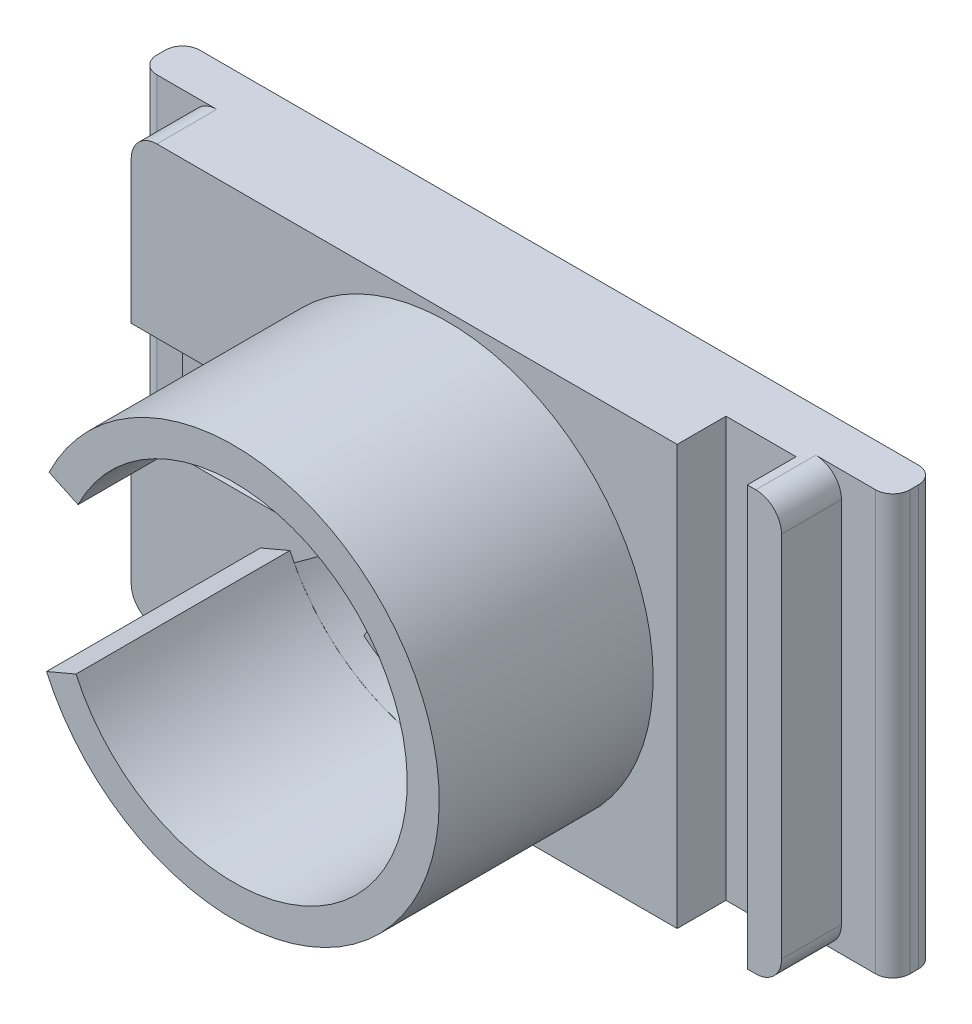
SolidWorks part; units mm, degrees
ref_plane "Front Plane" through (0, 0, 0) normal (0, 0, 1) x (1, 0, 0)
ref_plane "Top Plane" through (0, 0, 0) normal (0, 1, 0) x (1, 0, 0)
ref_plane "Right Plane" through (0, 0, 0) normal (1, 0, 0) x (0, 0, -1)
sketch "Sketch1" plane through (0, 0, 0) normal (0, 0, 1) x (1, 0, 0)
  line L1 (-32.5, -25) -> (32.5, -25)
  line L2 (-32.5, -25) -> (-32.5, 25)
  line L3 (-32.5, 25) -> (32.5, 25)
  line L4 (32.5, -25) -> (32.5, 25)
  line L5 (-32.5, -25) -> (32.5, 25) construction
  line L6 (-32.5, 25) -> (32.5, -25) construction
  point P0 (0, 0)
  dimension "D1" = 0
  dimension "D2" = 50
  dimension "D3" = 65
extrude "Boss-Extrude1" add sketch "Sketch1" along normal blind 12
sketch "Sketch2" plane through (0, 0, 12) normal (0, 0, 1) x (1, 0, 0)
  line L0 (32.5, -25) -> (32.5, 25) construction
  line L1 (-32.5, -25) -> (32.5, -25) construction
  line L2 (-1.6792, -18.9347) -> (-0.0792, -16.1634)
  line L3 (-44.0305, 5.35) -> (-14.0305, 5.35)
  line L4 (-44.0305, 5.35) -> (-44.0305, -5.35)
  line L5 (-44.0305, -5.35) -> (-14.0305, -5.35)
  line L6 (-14.0305, 5.35) -> (-14.0305, -5.35)
  line L7 (-7.3083, -15.6847) -> (-5.7083, -12.9134)
  line L8 (25.4875, 3.25) -> (22.2875, 3.25)
  line L9 (25.4875, 3.25) -> (25.4875, -3.25)
  line L10 (25.4875, -3.25) -> (22.2875, -3.25)
  line L11 (22.2875, 3.25) -> (22.2875, -3.25)
  line L12 (-0.0792, -16.1634) -> (-5.7083, -12.9134)
  line L13 (-7.3083, 15.6847) -> (-5.7083, 12.9134)
  line L14 (-1.6792, 18.9347) -> (-0.0792, 16.1634)
  line L15 (-5.7083, 12.9134) -> (-0.0792, 16.1634)
  line L16 (5.5, 0) -> (22.2875, -3.25) construction
  circle A0 centre (5.5, 0) radius 20.25
  point P25 (8, -1.4434)
  dimension "D1" = 20.25
  dimension "DK" = 40.5
  dimension "D2" = 27
  dimension "D3" = 25
  dimension "D4" = 20.25
  dimension "D5" = 30
  dimension "D6" = 10.7
  dimension "D7" = 20.25
  dimension "D8" = 20.25
  dimension "D9" = 6.5
  dimension "D10" = 3.2
  dimension "D11" = 3
  dimension "D12" = 17.0992
extrude "Cut-Extrude1" cut sketch "Sketch2" against normal blind 6
sketch "Sketch3" plane through (0, 0, 6) normal (0, 0, 1) x (1, 0, 0)
  circle A0 centre (5.5, 0) radius 9
  arc A1 (-1.6792, -18.9347) -> (25.4875, -3.25) centre (5.5, 0) ccw construction
  dimension "D2" = 18
  dimension "D1" = 0
extrude "Cut-Extrude2" cut sketch "Sketch3" against normal through all
sketch "Sketch4" plane through (0, 0, 12) normal (0, 0, 1) x (1, 0, 0)
  circle A0 centre (5.5, 0) radius 20.25
  arc A1 (-1.6792, -18.9347) -> (25.4875, -3.25) centre (5.5, 0) ccw construction
  dimension "D2" = 0
  dimension "D1" = 0
extrude "Cut-Extrude3" cut sketch "Sketch4" against normal blind 3
sketch "Sketch5" plane through (32.5, 0, 0) normal (1, 0, 0) x (0, 0, -1)
  line L0 (-12, -25) -> (-12, 25) construction
  line L1 (-12, -25) -> (0, -25)
  line L2 (-12, -25) -> (-12, 25)
  line L3 (-12, 25) -> (0, 25)
  line L4 (0, -25) -> (0, 25)
  line L5 (0, -25) -> (0, 25) construction
  line L6 (-12, 25) -> (0, 25) construction
  line L7 (-12, -25) -> (0, -25) construction
  dimension "D1" = 0
  dimension "D2" = 0
  dimension "D3" = 0
  dimension "D4" = 0
extrude "Boss-Extrude2" add sketch "Sketch5" along normal blind 13
sketch "Sketch6" plane through (0, 0, 12) normal (0, 0, 1) x (1, 0, 0)
  line L0 (-32.5, -25) -> (45.5, -25) construction
  line L1 (40.509, -25) -> (32.309, -25)
  line L2 (40.509, -25) -> (40.509, 25)
  line L3 (40.509, 25) -> (32.309, 25)
  line L4 (32.309, -25) -> (32.309, 25)
  line L5 (45.5, 25) -> (-32.5, 25) construction
  dimension "D1" = 0
  dimension "D2" = 8.2
  dimension "D3" = 0
extrude "Cut-Extrude4" cut sketch "Sketch6" against normal blind 5.7
sketch "Sketch7" plane through (45.5, 0, 0) normal (1, 0, 0) x (0, 0, -1)
  line L0 (-12, -25) -> (0, -25) construction
  line L1 (-5, -25) -> (0, -25)
  line L2 (-5, -25) -> (-5, 25)
  line L3 (-5, 25) -> (0, 25)
  line L4 (0, -25) -> (0, 25)
  line L5 (0, -25) -> (0, 25) construction
  line L6 (0, 25) -> (-12, 25) construction
  dimension "D1" = 0
  dimension "D2" = 0
  dimension "D3" = 0
  dimension "D4" = 5
extrude "Boss-Extrude3" add sketch "Sketch7" along normal blind 5
sketch "Sketch8" plane through (-32.5, 0, 0) normal (-1, 0, 0) x (0, 0, 1)
  line L0 (12, 25) -> (0, 25) construction
  line L1 (5, 25) -> (0, 25)
  line L2 (5, 25) -> (5, -25)
  line L3 (5, -25) -> (0, -25)
  line L4 (0, 25) -> (0, -25)
  line L5 (12, -25) -> (0, -25) construction
  line L6 (0, 25) -> (0, -25) construction
  dimension "D1" = 0
  dimension "D2" = 0
  dimension "D3" = 0
  dimension "D4" = 5
extrude "Boss-Extrude4" add sketch "Sketch8" along normal blind 5
fillet "Fillet1" radius 2 3 edges at (50.5, 0, 5)
fillet "Fillet2" radius 2 3 edges at (-37.5, 0, 5)
sketch "Sketch9" plane through (0, 0, 12) normal (0, 0, 1) x (1, 0, 0)
  line L0 (-12.47, 8.7795) -> (-16.093, 10.4759)
  line L1 (-12.7089, -8.2726) -> (-16.3918, -9.8362)
  circle A0 centre (5.5, 0) radius 20.26
  circle A1 centre (5.5, 0) radius 24
  arc A2 (-14.0305, -5.35) -> (-14.0305, 5.35) centre (5.5, 0) ccw construction
  dimension "D1" = 0
  dimension "D2" = 0
  dimension "D3" = 0.01
  dimension "D4" = 48
  dimension "D5" = 20
  dimension "D6" = 24
  dimension "D7" = 24
  dimension "D8" = 20
extrude "Boss-Extrude6" add sketch "Sketch9" along normal blind 25 contours L1 A1 L0 A0
fillet "Fillet3" radius 2 1 edges at (-37.5, 0, 0)
fillet "Fillet4" radius 2 1 edges at (50.5, 0, 0)
sketch "Sketch10" plane through (0, 0, 12) normal (0, 0, 1) x (1, 0, 0)
  line L0 (-32.5, 25) -> (-32.5, 5.35) construction
  line L1 (44.5, -25) -> (45.5, -25)
  line L2 (44.5, -25) -> (44.5, 25)
  line L3 (44.5, 25) -> (45.5, 25)
  line L4 (45.5, -25) -> (45.5, 25)
  line L5 (-32.5, -25) -> (-31.5, -25)
  line L6 (-32.5, -25) -> (-32.5, 25)
  line L7 (-32.5, 25) -> (-31.5, 25)
  line L8 (-31.5, -25) -> (-31.5, 25)
  line L13 (32.309, 25) -> (-32.5, 25) construction
  line L14 (-32.5, -25) -> (32.309, -25) construction
  line L17 (45.5, 25) -> (45.5, -25) construction
  line L18 (45.5, 25) -> (40.509, 25) construction
  dimension "D1" = 0
  dimension "D2" = 0
  dimension "D3" = 1
  dimension "D4" = 0
  dimension "D10" = 0
  dimension "D11" = 0
  dimension "D12" = 1
extrude "Cut-Extrude5" cut sketch "Sketch10" against normal blind 7
sketch "Sketch11" plane through (0, 0, 12) normal (0, 0, 1) x (1, 0, 0)
  line L0 (50.5, 25) -> (50.5, -25) construction
  line L1 (50.5, -25) -> (-37.5, -25)
  line L2 (50.5, -25) -> (50.5, -24)
  line L3 (50.5, -24) -> (-37.5, -24)
  line L4 (-37.5, -25) -> (-37.5, -24)
  line L5 (-37.5, -25) -> (-37.5, 25) construction
  line L6 (-31.5, -25) -> (32.309, -25) construction
  dimension "D1" = 0
  dimension "D2" = 0
  dimension "D3" = 0
  dimension "D4" = 1
extrude "Cut-Extrude6" cut sketch "Sketch11" against normal through all
fillet "Fillet5" radius 3 1 edges at (44.5, -24, 8.5)
fillet "Fillet6" radius 3 1 edges at (44.5, 25, 8.5)
fillet "Fillet7" radius 3 1 edges at (-31.5, 25, 8.5)
fillet "Fillet8" radius 3 1 edges at (-31.5, -24, 8.5)
